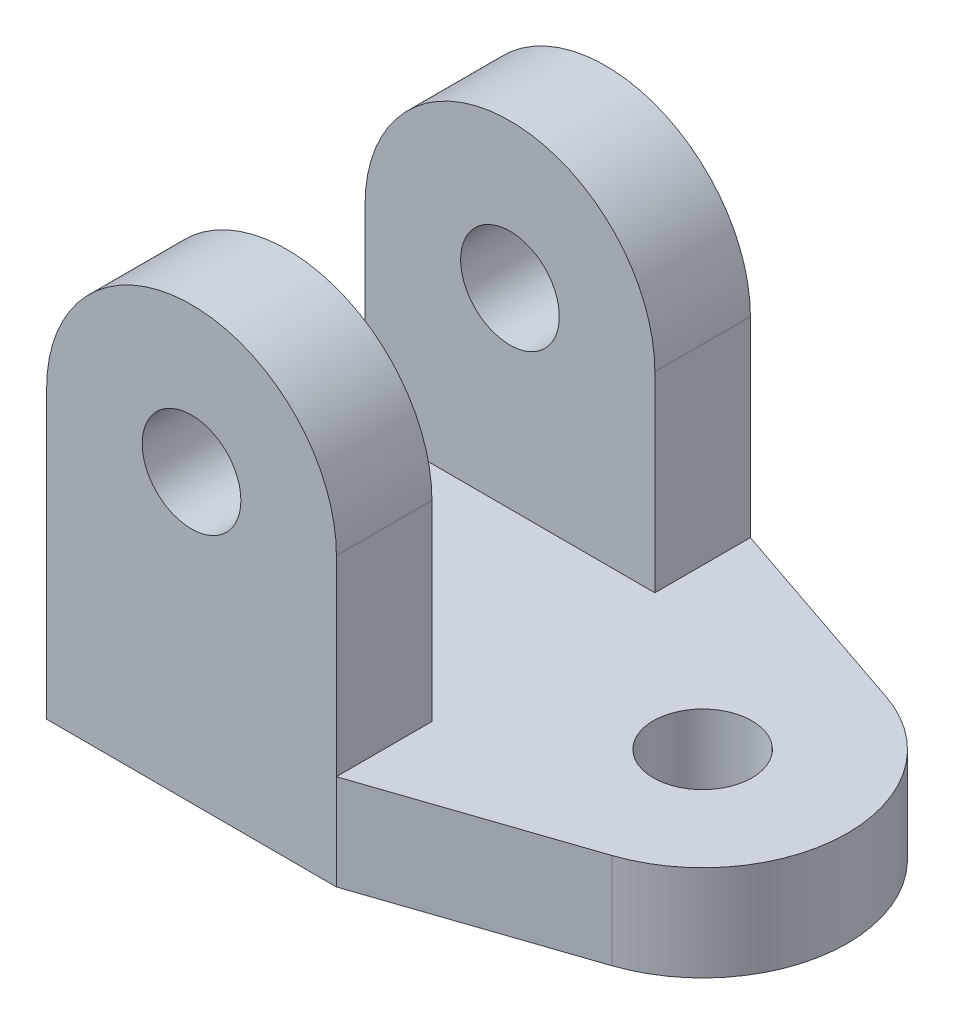
SolidWorks part; units mm, degrees
ref_plane "Front Plane" through (0, 0, 0) normal (0, 0, 1) x (1, 0, 0)
ref_plane "Top Plane" through (0, 0, 0) normal (0, 1, 0) x (1, 0, 0)
ref_plane "Right Plane" through (0, 0, 0) normal (1, 0, 0) x (0, 0, -1)
sketch "Sketch1" plane through (0, 0, 0) normal (0, 0, 1) x (1, 0, 0)
  line L0 (80.45, -5) -> (80.45, -11)
  line L1 (85, -5) -> (85, -11.0118) construction
  line L2 (89.55, -5) -> (89.55, -11.0118)
  line L3 (89.55, -11.0118) -> (80.45, -11)
  circle A1 centre (85, -5) radius 1.55
  circle A2 centre (85, -5) radius 4.55
  arc A4 (80.0471, -5.6849) -> (89.9529, -5.6849) centre (85, -5) ccw
  point P9 (85, -10)
  dimension "D1" = 3
  dimension "D2" = 1
extrude "Boss-Extrude1" add sketch "Sketch1" along normal blind 3
ref_plane "Plane1" through (0, 0, -7) normal (0, 0, -1) x (-1, 0, 0)
sketch "Sketch2" plane through (0, 0, -7) normal (0, 0, -1) x (-1, 0, 0)
  line L3 (-89.55, -11.0118) -> (-80.45, -11)
  line L4 (-89.55, -5) -> (-89.55, -11.0118)
  line L5 (-80.45, -11) -> (-80.45, -5)
  line L6 (-89.55, -11.0118) -> (-80.45, -11)
  line L7 (-89.55, -5) -> (-89.55, -11.0118)
  line L8 (-80.45, -11) -> (-80.45, -5)
  circle A0 centre (-85, -5) radius 1.55 construction
  arc A1 (-80.45, -5) -> (-89.55, -5) centre (-85, -5) ccw
  arc A2 (-80.45, -5) -> (-89.55, -5) centre (-85, -5) ccw
  circle A3 centre (-85, -5) radius 1.55
  dimension "D1" = 0
extrude "Boss-Extrude2" add sketch "Sketch2" along normal blind 3 separate body
sketch "Sketch3" plane through (-0.0141, -10.8958, 0) normal (-0.0013, -1, 0) x (1, -0.0013, 0)
  line L0 (89.5642, -3.5) -> (94.5642, -3.5) construction
  line L1 (80.4642, 3) -> (89.5642, 3)
  line L2 (80.4642, 3) -> (80.4642, -10)
  line L3 (80.4642, -10) -> (89.5642, -10)
  line L4 (89.5642, 3) -> (89.5642, -10)
  line L5 (89.5642, 3) -> (96.0254, 0.809)
  line L6 (89.5642, -10) -> (96.0254, -7.809)
  circle A0 centre (94.5642, -3.5) radius 1.55
  circle A1 centre (94.5642, -3.5) radius 4.55
  dimension "D2" = 3.1
  dimension "D3" = 3
  dimension "D1" = 5
extrude "Boss-Extrude3" add sketch "Sketch3" along normal blind 3
